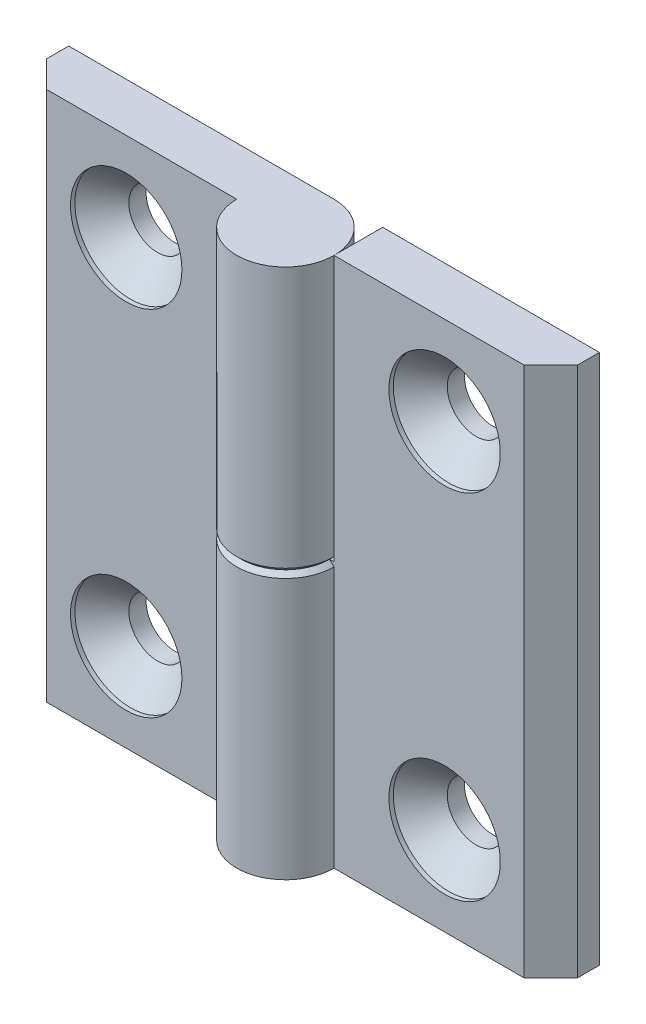
SolidWorks part; units mm, degrees
material "Алюминиевый сплав"
ref_plane "Спереди" through (0, 0, 0) normal (0, 0, 1) x (1, 0, 0)
ref_plane "Сверху" through (0, 0, 0) normal (0, 1, 0) x (1, 0, 0)
ref_plane "Справа" through (0, 0, 0) normal (1, 0, 0) x (0, 0, -1)
sketch "Эскиз1" plane through (0, 0, 0) normal (0, 1, 0) x (1, 0, 0)
  line L0 (0, 5.5) -> (-30, 5.5)
  line L1 (-30, 5.5) -> (-30, 3)
  line L2 (-30, 3) -> (-27, 0)
  line L3 (-27, 0) -> (-5.5, 0)
  line L4 (0, 0) -> (0, 10.5526) construction
  arc A0 (-5.5, 0) -> (0, 5.5) centre (0, 0) ccw
  dimension "D1" = 60
  dimension "D2" = 5.5
  dimension "D3" = 2.5
  dimension "D4" = 45
extrude "Бобышка-Вытянуть1" add sketch "Эскиз1" along normal mid plane 60
sketch "Эскиз3" plane through (0, 0, 0) normal (0, 0, 1) x (1, 0, 0)
  line L5 (-5.5, 30) -> (-5.5, -30) construction
  line L6 (5.5, -30) -> (-5.5, -30)
  line L7 (5.5, -30) -> (5.5, 0)
  line L8 (5.5, 0) -> (-5.5, 0)
  line L9 (-5.5, -30) -> (-5.5, 0)
extrude "Вырез-Вытянуть1" cut sketch "Эскиз3" against normal through all and the other way through all
hole_wizard "Зенковка для винта с полупотайной головкой M61" positions "Эскиз4" profile "Эскиз6" countersink size "M6" standard "ISO" end condition through all
sketch "Эскиз4" plane through (0, 0, 0) normal (0, 0, 1) x (1, 0, 0)
  line L0 (-18, 20) -> (-18, -20)
  line L2 (0, 0) -> (0, 18.9001) construction
  point P0 (-18, 20)
  point P2 (-18, -20)
  point P9 (-18, 0)
  dimension "D1" = 40
  dimension "D2" = 36
sketch "Эскиз6" plane through (-18, 20, 0) normal (1, 0, 0) x (0, -1, 0)
  line L0 (0, 0) -> (0, 5.5)
  line L1 (0, 5.5) -> (3.25, 5.5)
  line L2 (3.25, 5.5) -> (3.25, 3.55)
  line L3 (3.25, 3.55) -> (6.3, 0.5)
  line L4 (6.3, 0.5) -> (6.3, 0)
  line L6 (6.3, 0) -> (0, 0)
  line L7 (-3.25, 3.55) -> (-6.3, 0.5) construction
  line L11 (0, -6.35) -> (0, 107.95) construction
  dimension "Диаметр сквозного отверстия" = 6.5
  dimension "Глубина сквозного отверстия" = 5.5
  dimension "Диаметр зенковки" = 12.6
  dimension "Угол зенковки" = 90
  dimension "Утопленность" = 0.5
chamfer "Фаска1" distance 0.5 angle 45 2 edges at (-2.75, 0, -5.5) (3.8891, 0, 3.8891)
sketch "Угол раскрытия" plane through (0, 0, 0) normal (0, 1, 0) x (1, 0, 0)
  line L0 (0, 0) -> (0, -10)
  line L7 (0, 5.5) -> (-30, 5.5) construction
  dimension "D1" = 10
  dimension "D2" = 90
pattern_circular "Круговой массив1" count 2 over 360 about axis through (0, 0, 0) along (0, 0, 1) of bodies 106
